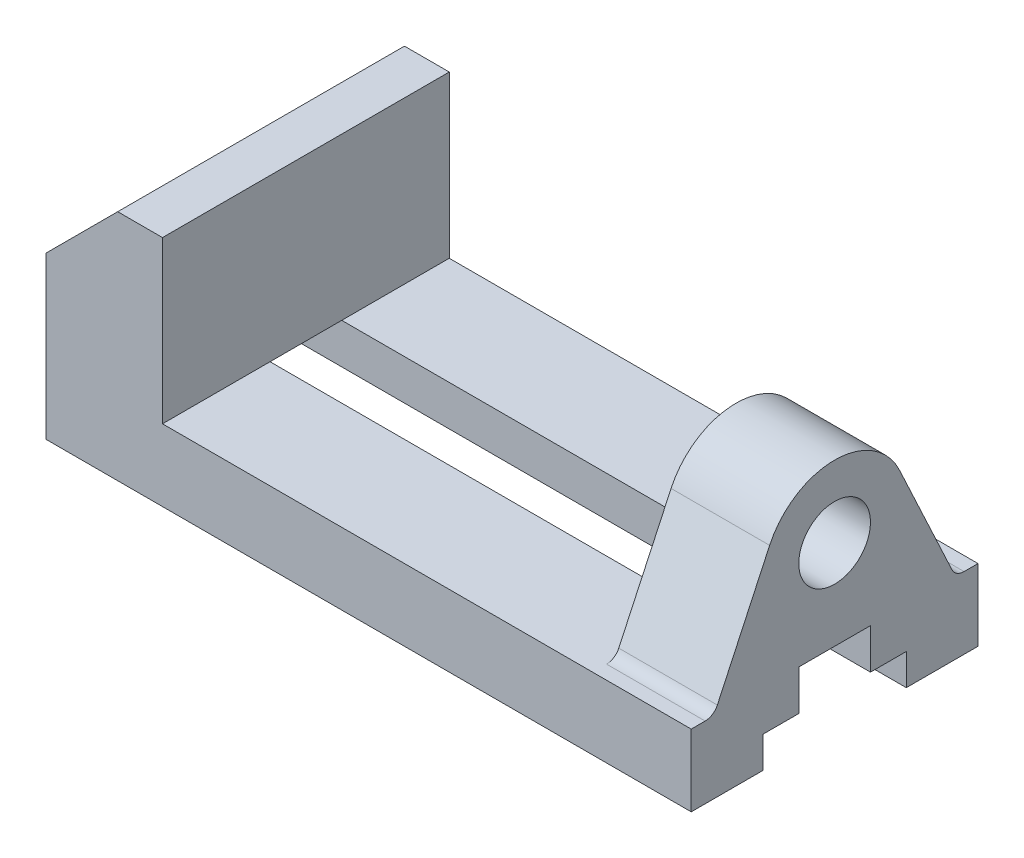
SolidWorks part; units mm, degrees
ref_plane "Front Plane" through (0, 0, 0) normal (0, 0, 1) x (1, 0, 0)
ref_plane "Top Plane" through (0, 0, 0) normal (0, 1, 0) x (1, 0, 0)
ref_plane "Right Plane" through (0, 0, 0) normal (1, 0, 0) x (0, 0, -1)
sketch "Sketch1" plane through (0, 0, 0) normal (0, 0, 1) x (1, 0, 0)
  line L0 (0, 0) -> (144, 0)
  line L1 (144, 0) -> (144, 52)
  line L2 (144, 52) -> (122, 52)
  line L3 (122, 52) -> (122, 16)
  line L4 (122, 16) -> (26, 16)
  line L5 (26, 16) -> (26, 52)
  line L6 (26, 52) -> (16, 52)
  line L7 (16, 52) -> (0, 36)
  line L8 (0, 36) -> (0, 0)
  dimension "D1" = 144
  dimension "D2" = 22
  dimension "D3" = 16
  dimension "D4" = 36
  dimension "D5" = 16
  dimension "D6" = 16
  dimension "D7" = 10
extrude "Boss-Extrude1" add sketch "Sketch1" along normal blind 64
sketch "Sketch2" plane through (144, 0, 0) normal (1, 0, 0) x (0, 0, -1)
  line L0 (-64, 52) -> (0, 52) construction
  line L1 (-64, 0) -> (0, 0) construction
  line L2 (-64, 16) -> (-60.8914, 16)
  line L3 (-46.5009, 42.7619) -> (-58.1725, 17.7321)
  line L4 (-17.4991, 42.7619) -> (-5.8275, 17.7321)
  line L5 (-32, 36) -> (-32, -22.6901) construction
  line L6 (-64, 0) -> (-64, 52) construction
  line L7 (0, 0) -> (0, 52) construction
  line L8 (0, 16) -> (0, 52)
  line L9 (-64, 52) -> (0, 52)
  line L10 (-3.1086, 16) -> (0, 16)
  line L12 (-64, 16) -> (-64, 52)
  circle A0 centre (-32, 36) radius 8
  circle A1 centre (-32, 36) radius 16
  arc A2 (-3.1086, 16) -> (-5.8275, 17.7321) centre (-3.1086, 19) cw
  arc A3 (-60.8914, 16) -> (-58.1725, 17.7321) centre (-60.8914, 19) ccw
  point P4 (-32, 52)
  point P11 (-5.0198, 16)
  dimension "D1" = 36
  dimension "D2" = 16
  dimension "D3" = 32
  dimension "D6" = 3
  dimension "D4" = 16
  dimension "D5" = 50
extrude "Cut-Extrude1" cut sketch "Sketch2" against normal blind 64
sketch "Sketch3" plane through (144, 0, 0) normal (1, 0, 0) x (0, 0, -1)
  line L0 (-64, 0) -> (0, 0) construction
  line L1 (-48, 0) -> (-16, 0)
  line L2 (-48, 0) -> (-48, 7)
  line L3 (-48, 7) -> (-40, 7)
  line L4 (-16, 0) -> (-16, 7)
  line L5 (-32, -7.9184) -> (-32, 21.6067) construction
  line L6 (-64, 0) -> (-64, 16) construction
  line L7 (0, 0) -> (0, 16) construction
  line L8 (-40, 7) -> (-40, 16)
  line L9 (-40, 16) -> (-24, 16)
  line L10 (-24, 16) -> (-24, 7)
  line L11 (-24, 7) -> (-16, 7)
  dimension "D1" = 32
  dimension "D2" = 7
  dimension "D3" = 16
  dimension "D4" = 16
extrude "Cut-Extrude2" cut sketch "Sketch3" against normal up to next
sketch "Sketch4" plane through (0, 0, 0) normal (0, -1, 0) x (1, 0, 0)
  line L0 (144, 16) -> (144, 0) construction
  line L1 (0, 0) -> (144, 0) construction
  line L2 (0, 64) -> (144, 64) construction
  circle A0 centre (36, 54) radius 3
  circle A1 centre (106, 54) radius 3
  circle A2 centre (36, 10) radius 3
  circle A3 centre (106, 10) radius 3
  point P12 (0, 0)
  point P13 (0, 0)
  point P16 (0, 0)
  point P17 (0, 0)
  dimension "D1" = 70
  dimension "D5" = 6
  dimension "D2" = 38
  dimension "D3" = 10
  dimension "D4" = 10
extrude "Cut-Extrude3" cut sketch "Sketch4" against normal blind 10
